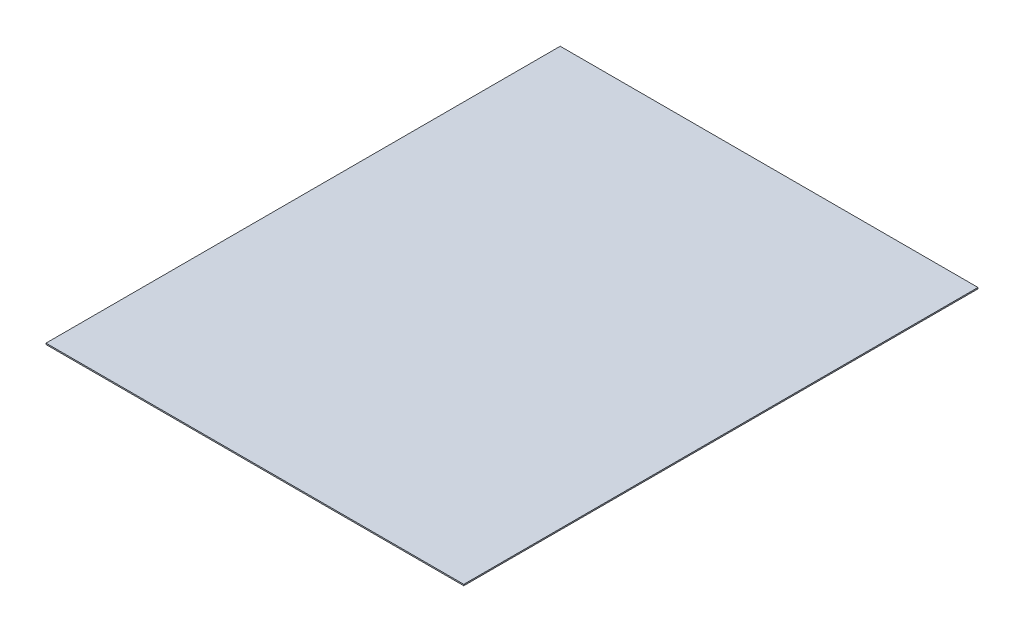
SolidWorks part; units mm, degrees
material "Acrylic (Medium-high impact)"
ref_plane "Front Plane" through (0, 0, 0) normal (0, 0, 1) x (1, 0, 0)
ref_plane "Top Plane" through (0, 0, 0) normal (0, 1, 0) x (1, 0, 0)
ref_plane "Right Plane" through (0, 0, 0) normal (1, 0, 0) x (0, 0, -1)
sketch "Sketch1" plane through (0, 0, 0) normal (0, 1, 0) x (1, 0, 0)
  line L1 (-495.3, 609.6) -> (495.3, 609.6)
  line L2 (-495.3, 609.6) -> (-495.3, -609.6)
  line L3 (-495.3, -609.6) -> (495.3, -609.6)
  line L4 (495.3, 609.6) -> (495.3, -609.6)
  line L5 (-495.3, 609.6) -> (495.3, -609.6) construction
  line L6 (-495.3, -609.6) -> (495.3, 609.6) construction
  point P0 (0, 0)
  dimension "D1" = 990.6
  dimension "D2" = 1219.2
extrude "Boss-Extrude1" add sketch "Sketch1" along normal blind 2.9972
